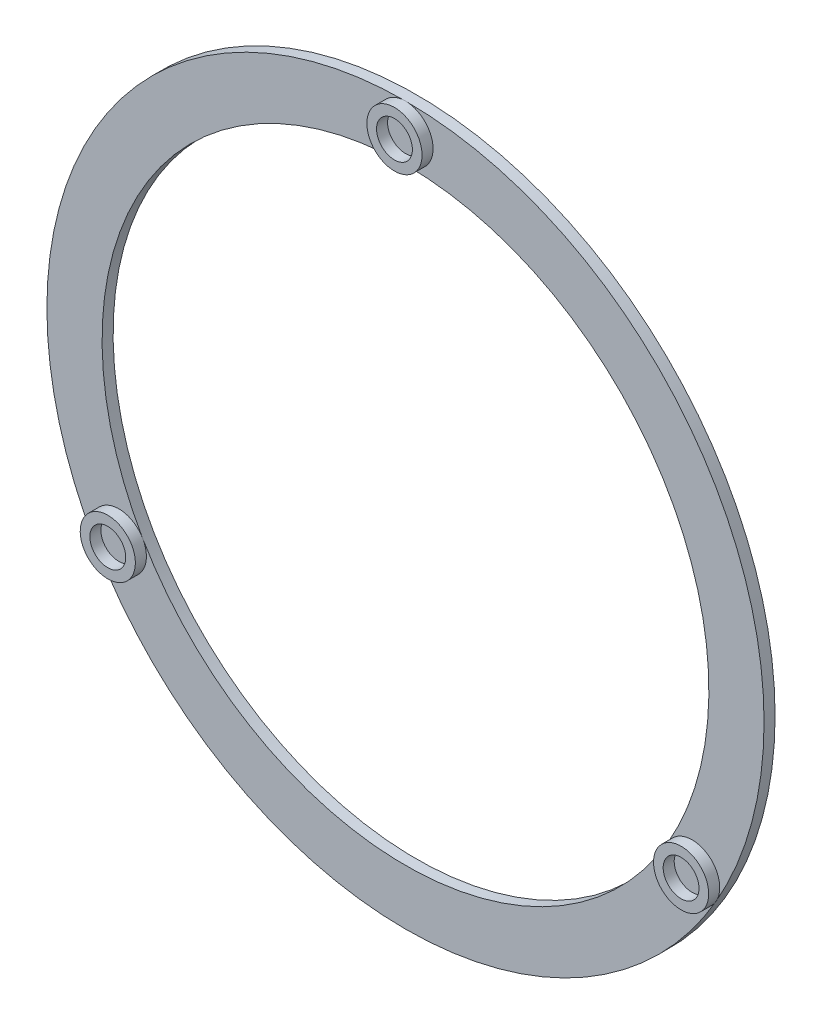
SolidWorks part; units mm, degrees
ref_plane "Front Plane" through (0, 0, 0) normal (0, 0, 1) x (1, 0, 0)
ref_plane "Top Plane" through (0, 0, 0) normal (0, 1, 0) x (1, 0, 0)
ref_plane "Right Plane" through (0, 0, 0) normal (1, 0, 0) x (0, 0, -1)
sketch "Sketch1" plane through (0, 0, 0) normal (0, 0, 1) x (1, 0, 0)
  circle A0 centre (0, 0) radius 275
  circle A1 centre (0, 0) radius 325
  circle A2 centre (0, 0) radius 300 construction
  dimension "D1" = 650
  dimension "D2" = 550
extrude "Boss-Extrude1" add sketch "Sketch1" along normal blind 10
sketch "Sketch2" plane through (0, 0, 10) normal (0, 0, 1) x (1, 0, 0)
  line L0 (281.4583, -162.5) -> (238.157, -137.5) construction
  line L1 (0, 325) -> (0, 275) construction
  line L2 (-281.4583, -162.5) -> (-238.157, -137.5) construction
  circle A0 centre (0, 0) radius 275 construction
  circle A1 centre (0, 300) radius 16.25
  circle A4 centre (0, 300) radius 25
  circle A11 centre (259.8076, -150) radius 16.25
  circle A12 centre (259.8076, -150) radius 25
  circle A13 centre (-259.8076, -150) radius 16.25
  circle A14 centre (-259.8076, -150) radius 25
  point P19 (0, 0)
  dimension "D3" = 50
  dimension "D5" = 32.5
extrude "Boss-Extrude2" add sketch "Sketch2" along normal blind 10
